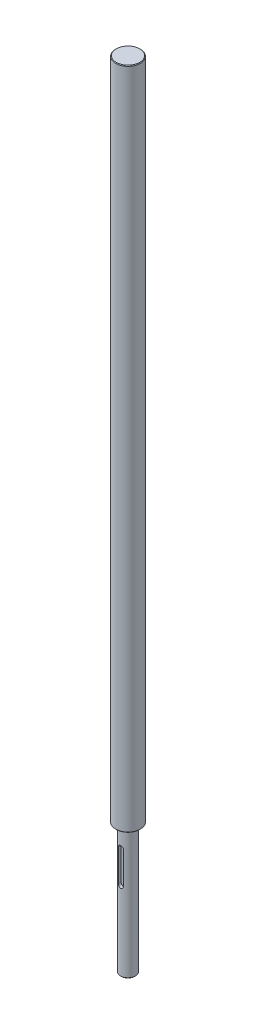
SolidWorks part; units mm, degrees
material "1.4301"
ref_plane "Ebene oben" through (0, 0, 0) normal (0, 0, 1) x (1, 0, 0)
ref_plane "Ebene vorne" through (0, 0, 0) normal (0, 1, 0) x (1, 0, 0)
ref_plane "Ebene rechts" through (0, 0, 0) normal (1, 0, 0) x (0, 0, -1)
sketch "Skizze1" plane through (0, 0, 0) normal (0, 1, 0) x (1, 0, 0)
  circle A0 centre (0, 0) radius 10
  dimension "D1" = 20
extrude "Aufsatz-Linear austragen1" add sketch "Skizze1" along normal blind 538
sketch "Skizze2" plane through (0, 0, 0) normal (0, -1, 0) x (1, 0, 0)
  circle A0 centre (0, 0) radius 6
  dimension "D1" = 12
extrude "Aufsatz-Linear austragen2" add sketch "Skizze2" along normal blind 105
chamfer "Fase1" distance 0.5 angle 45 3 edges at (0, 538, 10) (0, -105, -6) (0, 0, 10)
sketch "Sketch2" plane through (-3.4136, -105, 0.7109) normal (0, -1, 0) x (1, 0, 0)
  line L0 (3.4136, 5.2891) -> (3.4136, -0.7109) construction
  line L1 (3.4136, -0.7109) -> (3.4136, 5.2891) construction
  circle A0 centre (3.4136, -0.7109) radius 6 construction
  circle A2 centre (3.4136, -0.7109) radius 6
  dimension "Angle from vertical" = 360
ref_plane "Plane1" through (0, -105, 6) normal (0, 0, -1) x (-1, 0, 0)
sketch "Sketch3" plane through (1.7068, -105, 6) normal (0, 0, -1) x (0, -1, 0)
  line L0 (-64, 1.7068) -> (-90, 1.7068) construction
  line L1 (-64, 3.7068) -> (-90, 3.7068)
  line L2 (-64, -0.2932) -> (-90, -0.2932)
  arc A0 (-64, 3.7068) -> (-64, -0.2932) centre (-64, 1.7068) cw
  arc A1 (-90, 3.7068) -> (-90, -0.2932) centre (-90, 1.7068) ccw
  dimension "Keyway width" = 4
  dimension "Distance from end face" = 64
  dimension "Length of slot" = 26
extrude "Cut-Extrude1" cut sketch "Sketch3" along normal blind 2.5
other "keyway (bs 4235 - part i)<1>"
